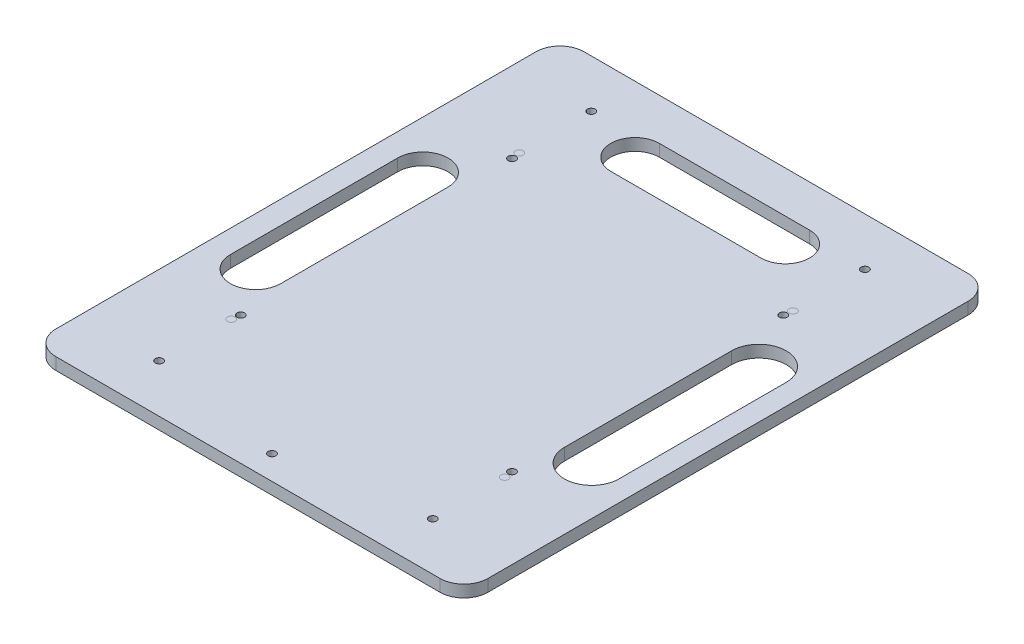
SolidWorks part; units mm, degrees
ref_plane "前视基准面" through (0, 0, 0) normal (0, 0, 1) x (1, 0, 0)
ref_plane "上视基准面" through (0, 0, 0) normal (0, 1, 0) x (1, 0, 0)
ref_plane "右视基准面" through (0, 0, 0) normal (1, 0, 0) x (0, 0, -1)
sketch "草图1" plane through (0, 0, 0) normal (0, 1, 0) x (1, 0, 0)
  line L0 (-114.0741, 75.3411) -> (-81.0741, 75.3411) construction
  line L1 (-104.0741, 85.3411) -> (55.9259, 85.3411)
  line L2 (-114.0741, 75.3411) -> (-114.0741, -124.6589)
  line L3 (-104.0741, -134.6589) -> (55.9259, -134.6589)
  line L4 (65.9259, 75.3411) -> (65.9259, -124.6589)
  line L5 (65.9259, 75.3411) -> (32.9259, 75.3411) construction
  line L6 (-114.0741, -124.6589) -> (-81.0741, -124.6589) construction
  line L7 (65.9259, -124.6589) -> (32.9259, -124.6589) construction
  line L8 (-81.0741, 85.3411) -> (-81.0741, 35.3411) construction
  line L9 (-81.0741, -134.6589) -> (-81.0741, -84.6589) construction
  line L10 (-81.0741, 35.3411) -> (32.9259, 35.3411) construction
  line L11 (32.9259, 35.3411) -> (32.9259, -84.6589) construction
  arc A0 (-104.0741, 85.3411) -> (-114.0741, 75.3411) centre (-104.0741, 75.3411) ccw
  arc A1 (55.9259, 85.3411) -> (65.9259, 75.3411) centre (55.9259, 75.3411) cw
  arc A2 (55.9259, -134.6589) -> (65.9259, -124.6589) centre (55.9259, -124.6589) ccw
  arc A3 (-114.0741, -124.6589) -> (-104.0741, -134.6589) centre (-104.0741, -124.6589) ccw
  circle A4 centre (-81.0741, 35.3411) radius 1.6
  circle A5 centre (32.9259, 35.3411) radius 1.6
  circle A6 centre (32.9259, -84.6589) radius 1.6
  circle A7 centre (-81.0741, -84.6589) radius 1.6
  point P6 (-114.0741, 85.3411)
  point P9 (65.9259, 85.3411)
  point P14 (-114.0741, -134.6589)
  dimension "D3" = 10
  dimension "D4" = 10
  dimension "D5" = 10
  dimension "D6" = 10
  dimension "D1" = 220
  dimension "D2" = 180
  dimension "D7" = 33
extrude "凸台-拉伸1" add sketch "草图1" along normal blind 5
sketch "草图4" plane through (0, 5, 0) normal (0, 1, 0) x (1, 0, 0)
  line L0 (-24.0741, 85.3411) -> (-24.0741, 75.3411) construction
  line L1 (55.9259, 85.3411) -> (-104.0741, 85.3411) construction
  line L2 (-24.0741, 85.3411) -> (-24.0741, -134.6589) construction
  line L3 (-104.0741, -134.6589) -> (55.9259, -134.6589) construction
  line L4 (65.9259, -24.6589) -> (-114.0741, -24.6589) construction
  line L5 (65.9259, -124.6589) -> (65.9259, 75.3411) construction
  line L6 (-114.0741, 75.3411) -> (-114.0741, -124.6589) construction
  line L7 (-24.0741, -24.6589) -> (32.6259, -24.6589) construction
  line L8 (-24.0741, -24.6589) -> (-80.7741, -24.6589) construction
  line L9 (-24.0741, -24.6589) -> (-24.0741, 31.8411) construction
  line L10 (-24.0741, 31.8411) -> (32.6259, 31.8411) construction
  line L11 (32.6259, 31.8411) -> (32.6259, -24.6589) construction
  line L12 (-24.0741, -24.6589) -> (-24.0741, -81.1589) construction
  line L13 (-24.0741, -81.1589) -> (32.6259, -81.1589) construction
  line L14 (32.6259, -81.1589) -> (32.6259, -24.6589) construction
  line L15 (32.6259, -24.6589) -> (-80.7741, -24.6589) construction
  line L16 (-80.7741, -24.6589) -> (-80.7741, -81.1589) construction
  line L17 (-80.7741, -81.1589) -> (-24.0741, -81.1589) construction
  line L18 (-80.7741, -24.6589) -> (-80.7741, 31.8411) construction
  line L19 (-80.7741, 31.8411) -> (-24.0741, 31.8411) construction
  line L20 (-81.0741, 35.3411) -> (-81.0741, 65.3411) construction
  line L21 (32.9259, 35.3411) -> (32.9259, 65.3411)
  line L22 (-81.0741, -84.6589) -> (-81.0741, -114.6589) construction
  line L23 (32.9259, -84.6589) -> (32.9259, -114.6589) construction
  circle A0 centre (-24.0741, 75.3411) radius 1.6
  circle A1 centre (-81.0741, 65.3411) radius 1.6
  circle A2 centre (32.9259, 65.3411) radius 1.6
  circle A3 centre (-81.0741, -114.6589) radius 1.6
  circle A4 centre (32.9259, -114.6589) radius 1.6
  circle A5 centre (-81.0741, 35.3411) radius 1.6
  circle A6 centre (32.9259, 35.3411) radius 1.6
  circle A7 centre (32.9259, -84.6589) radius 1.6
  circle A8 centre (-81.0741, -84.6589) radius 1.6
  circle A9 centre (-80.7741, 31.8411) radius 1.6
  circle A10 centre (32.6259, 31.8411) radius 1.6
  circle A11 centre (32.6259, -81.1589) radius 1.6
  circle A12 centre (-80.7741, -81.1589) radius 1.6
  dimension "D1" = 3.2
  dimension "D2" = 56.7
extrude "切除-拉伸2" cut sketch "草图4" against normal blind 10 contours A3 | A4 | A2 | A1
sketch "草图5" plane through (0, 5, 0) normal (0, 1, 0) x (1, 0, 0)
  circle A0 centre (-81.0741, 35.3411) radius 1.6
  circle A1 centre (32.9259, 35.3411) radius 1.6
  circle A2 centre (32.9259, -84.6589) radius 1.6
  circle A3 centre (-81.0741, -84.6589) radius 1.6
extrude "凸台-拉伸3" add sketch "草图5" against normal blind 5 separate body
sketch "草图6" plane through (0, 5, 0) normal (0, 1, 0) x (1, 0, 0)
  line L0 (-24.0741, 85.3411) -> (-24.0741, -134.6589) construction
  line L1 (55.9259, 85.3411) -> (-104.0741, 85.3411) construction
  line L2 (-104.0741, -134.6589) -> (55.9259, -134.6589) construction
  line L3 (-24.0741, -134.6589) -> (-114.0741, -24.6589) construction
  line L4 (-114.0741, 75.3411) -> (-114.0741, -124.6589) construction
  line L5 (-114.0741, -24.6589) -> (65.9259, -24.6589) construction
  line L6 (65.9259, -124.6589) -> (65.9259, 75.3411) construction
  line L7 (-24.0741, -24.6589) -> (32.4259, -24.6589) construction
  line L8 (-24.0741, -24.6589) -> (-80.5741, -24.6589) construction
  line L9 (-24.0741, -24.6589) -> (-24.0741, 31.8411) construction
  line L10 (-24.0741, -24.6589) -> (-24.0741, -81.1589) construction
  line L11 (-24.0741, 31.8411) -> (32.4259, 31.8411) construction
  line L12 (32.4259, 31.8411) -> (32.4259, -24.6589) construction
  line L13 (-24.0741, -81.1589) -> (-80.5741, -81.1589) construction
  line L14 (-80.5741, -81.1589) -> (-80.5741, -24.6589) construction
  line L15 (-24.0741, -81.1589) -> (32.4259, -81.1589) construction
  line L16 (32.4259, -81.1589) -> (32.4259, -24.6589) construction
  line L17 (-24.0741, 31.8411) -> (-80.5741, 31.8411) construction
  line L18 (-80.5741, 31.8411) -> (-80.5741, -24.6589) construction
  circle A0 centre (-80.5741, -81.1589) radius 1.6
  circle A1 centre (-80.5741, 31.8411) radius 1.6
  circle A2 centre (32.4259, 31.8411) radius 1.6
  circle A3 centre (32.4259, -81.1589) radius 1.6
extrude "切除-拉伸3" cut sketch "草图6" against normal blind 5
sketch "草图8" plane through (0, 0, 0) normal (0, -1, 0) x (1, 0, 0)
  line L0 (-24.0741, 134.6589) -> (-24.0741, 124.6589) construction
  line L1 (-104.0741, 134.6589) -> (55.9259, 134.6589) construction
  circle A0 centre (-24.0741, 124.6589) radius 1.6
extrude "切除-拉伸4" cut sketch "草图8" against normal blind 5
sketch "草图9" plane through (0, 0, 0) normal (0, -1, 0) x (1, 0, 0)
  line L0 (-114.0741, 24.6589) -> (65.9259, 24.6589) construction
  line L1 (-114.0741, -75.3411) -> (-114.0741, 124.6589) construction
  line L2 (65.9259, 124.6589) -> (65.9259, -75.3411) construction
  line L3 (-24.0741, 134.6589) -> (-24.0741, -85.3411) construction
  line L4 (-104.0741, 134.6589) -> (55.9259, 134.6589) construction
  line L5 (55.9259, -85.3411) -> (-104.0741, -85.3411) construction
  line L6 (-114.0741, 24.6589) -> (-94.0741, 24.6589) construction
  line L7 (65.9259, 24.6589) -> (45.9259, 24.6589) construction
  line L8 (-94.0741, 61.4612) -> (-94.0741, -8.2026) construction
  line L9 (-83.5838, 61.4612) -> (-83.5838, -8.2026)
  line L10 (-104.5644, 61.4612) -> (-104.5644, -8.2026)
  line L11 (45.9259, 61.4612) -> (45.9259, -8.2026) construction
  line L12 (57.3035, 61.4612) -> (57.3035, -8.2026)
  line L13 (34.5483, 61.4612) -> (34.5483, -8.2026)
  line L14 (-55.3481, -57.8722) -> (7.2271, -57.8722) construction
  line L15 (-55.3481, -47.7637) -> (7.2271, -47.7637)
  line L16 (-55.3481, -67.9807) -> (7.2271, -67.9807)
  arc A0 (-83.5838, 61.4612) -> (-104.5644, 61.4612) centre (-94.0741, 61.4612) ccw
  arc A1 (-104.5644, -8.2026) -> (-83.5838, -8.2026) centre (-94.0741, -8.2026) ccw
  arc A2 (57.3035, 61.4612) -> (34.5483, 61.4612) centre (45.9259, 61.4612) ccw
  arc A3 (34.5483, -8.2026) -> (57.3035, -8.2026) centre (45.9259, -8.2026) ccw
  arc A4 (-55.3481, -47.7637) -> (-55.3481, -67.9807) centre (-55.3481, -57.8722) ccw
  arc A5 (7.2271, -67.9807) -> (7.2271, -47.7637) centre (7.2271, -57.8722) ccw
  point P16 (-94.0741, 26.6293)
  point P21 (45.9259, 26.6293)
  point P30 (-24.0605, -57.8722)
extrude "切除-拉伸5" cut sketch "草图9" against normal blind 10
